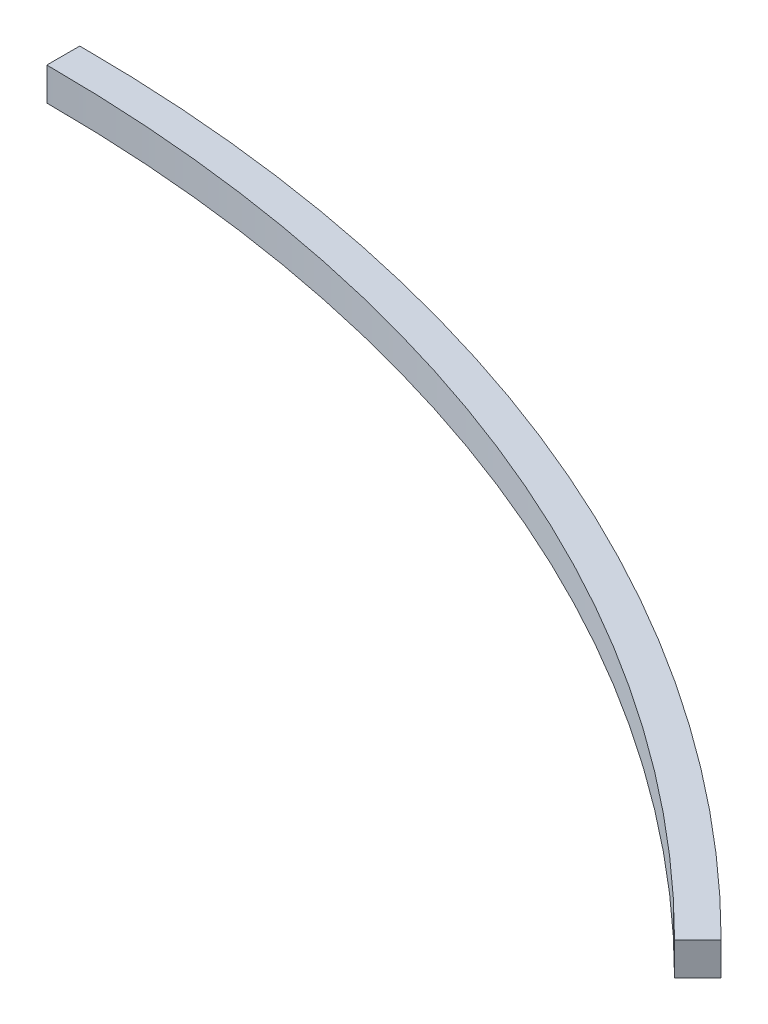
SolidWorks part; units mm, degrees
ref_plane "Front Plane" through (0, 0, 0) normal (0, 0, 1) x (1, 0, 0)
ref_plane "Top Plane" through (0, 0, 0) normal (0, 1, 0) x (1, 0, 0)
ref_plane "Right Plane" through (0, 0, 0) normal (1, 0, 0) x (0, 0, -1)
sketch "Sketch1" plane through (0, 0, 0) normal (0, 1, 0) x (1, 0, 0)
  line L0 (0, 0) -> (0, 460) construction
  line L1 (0, 460) -> (0, 470)
  line L2 (0, 0) -> (332.3402, 332.3402) construction
  line L3 (325.2691, 325.2691) -> (332.3402, 332.3402)
  arc A0 (0, 460) -> (325.2691, 325.2691) centre (0, 0) cw
  arc A1 (0, 470) -> (332.3402, 332.3402) centre (0, 0) cw
  dimension "D1" = 460
  dimension "D2" = 10
  dimension "D3" = 45
  dimension "D4" = 470
extrude "Boss-Extrude1" add sketch "Sketch1" along normal blind 10 contours A1 L1 A0 L3
